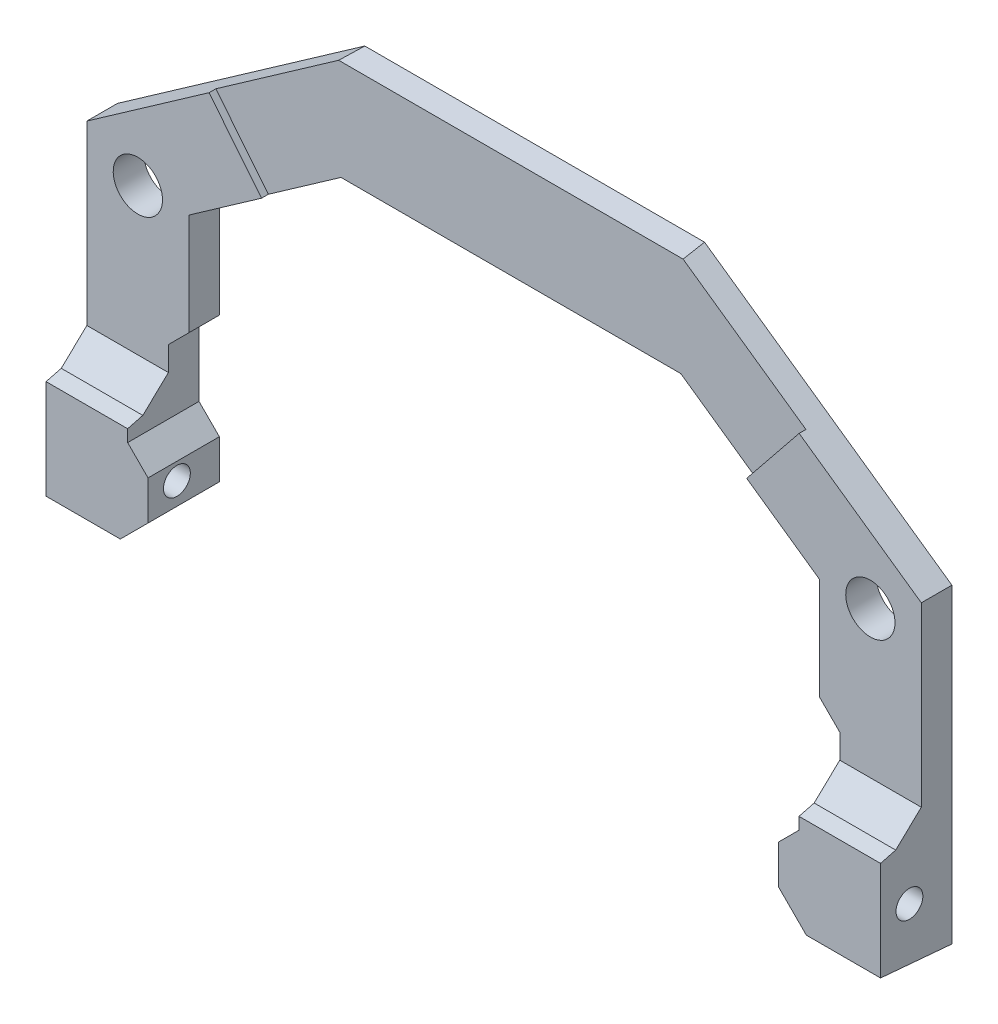
SolidWorks part; units mm, degrees
ref_plane "Front Plane" through (0, 0, 0) normal (0, 0, 1) x (1, 0, 0)
ref_plane "Top Plane" through (0, 0, 0) normal (0, 1, 0) x (1, 0, 0)
ref_plane "Right Plane" through (0, 0, 0) normal (1, 0, 0) x (0, 0, -1)
sketch "Sketch1" plane through (0, 0, 0) normal (0, 0, 1) x (1, 0, 0)
  line L0 (0, 0) -> (-31.1912, 0)
  line L1 (-31.1912, 0) -> (-31.1912, -36.195)
  line L2 (-31.1912, -36.195) -> (-23.5712, -36.195)
  line L3 (-23.5712, -36.195) -> (-23.5712, -7.62)
  line L4 (-23.5712, -7.62) -> (0, -7.62)
  line L5 (0, -7.62) -> (0, 0)
  dimension "D1" = 7.62
  dimension "D2" = 7.62
  dimension "D3" = 23.5712
  dimension "D4" = 28.575
extrude "Boss-Extrude1" add sketch "Sketch1" along normal blind 6.35
sketch "Sketch2" plane through (-23.5712, 0, 0) normal (1, 0, 0) x (0, 0, -1)
  line L0 (-3.175, -36.195) -> (-3.175, -20.616) construction
  line L1 (-6.35, -36.195) -> (0, -36.195) construction
  line L2 (-6.35, -7.62) -> (0, -7.62) construction
  circle A0 centre (-3.175, -32.004) radius 1.0033
  dimension "D1" = 2.0066
  dimension "D2" = 24.384
extrude "cut for lid mount screw" cut sketch "Sketch2" against normal through all and the other way through all
sketch "Sketch3" plane through (0, 0, 6.35) normal (0, 0, 1) x (1, 0, 0)
  line L0 (-27.3812, -36.195) -> (-27.3812, 2.9312) construction
  line L1 (-31.1912, -36.195) -> (-23.5712, -36.195) construction
  line L2 (0, 0) -> (-31.1912, 0) construction
  circle A0 centre (-27.3812, -15.24) radius 1.8415
  dimension "D1" = 3.683
  dimension "D2" = 15.24
extrude "cut for mounting screw" cut sketch "Sketch3" against normal through all
mirror "Mirror1" about plane through (0, 0, 0) normal (1, 0, 0) of "Boss-Extrude1"
mirror "Mirror2" about plane through (0, 0, 0) normal (1, 0, 0) of "cut for lid mount screw"
mirror "Mirror3" about plane through (0, 0, 0) normal (1, 0, 0) of "cut for mounting screw"
sketch "Sketch4" plane through (0, 0, 6.35) normal (0, 0, 1) x (1, 0, 0)
  line L0 (-25.0952, -24.384) -> (-25.0952, -29.2079)
  line L1 (-23.5712, -36.195) -> (-23.5712, -7.62) construction
  line L2 (-25.0952, -29.2079) -> (-23.5712, -30.7319)
  line L3 (-23.5712, -22.86) -> (-23.5712, -30.7319)
  line L4 (-23.5712, -36.195) -> (-23.5712, -33.655)
  line L7 (-25.0952, -24.384) -> (-23.5712, -22.86)
  line L8 (-23.5712, -33.655) -> (-26.1112, -36.195)
  line L10 (-23.5712, -7.62) -> (23.5712, -7.62) construction
  line L11 (-31.1912, -36.195) -> (-23.5712, -36.195) construction
  line L12 (-26.1112, -36.195) -> (-23.5712, -36.195)
  dimension "D1" = 135
  dimension "D2" = 135
  dimension "D3" = 1.524
  dimension "D4" = 15.24
  dimension "D5" = 2.54
  dimension "D6" = 2.54
extrude "cut for control wire clearance" cut sketch "Sketch4" against normal through all
mirror "Mirror4" about plane through (0, 0, 0) normal (1, 0, 0) of "cut for control wire clearance"
sketch "Sketch5" plane through (0, 0, 6.35) normal (0, 0, 1) x (1, 0, 0)
  line L0 (-23.5712, -15.24) -> (-12.7, -7.62)
  line L1 (-23.5712, -22.86) -> (-23.5712, -7.62) construction
  line L2 (-23.5712, -7.62) -> (23.5712, -7.62) construction
  line L3 (-31.1912, -12.5421) -> (-13.2978, 0)
  line L4 (-31.1912, 0) -> (-31.1912, -36.195) construction
  line L5 (31.1912, 0) -> (-31.1912, 0) construction
  line L6 (-12.7, -7.62) -> (-13.2978, 0)
  line L7 (-31.1912, -12.5421) -> (-25.1687, -12.5421)
  line L8 (-25.1687, -12.5421) -> (-23.5712, -15.24)
  point P6 (0, -7.62)
  dimension "D1" = 12.7
extrude "Boss-Extrude2" add sketch "Sketch5" against normal blind 6.35
sketch "Sketch6" plane through (0, 0, 6.35) normal (0, 0, 1) x (1, 0, 0)
  line L0 (-12.7, 0) -> (-31.1912, -12.9611)
  line L1 (31.1912, 0) -> (-31.1912, 0) construction
  line L2 (-31.1912, 0) -> (-31.1912, -36.195) construction
  line L3 (-31.1912, -12.9611) -> (-31.1912, 0)
  line L4 (-31.1912, 0) -> (-12.7, 0)
  line L5 (-23.5712, -15.24) -> (-12.7, -7.62) construction
extrude "Cut-Extrude1" cut sketch "Sketch6" against normal through all
mirror "Mirror5" about plane through (0, 0, 0) normal (1, 0, 0) of "Cut-Extrude1", "Boss-Extrude2"
sketch "Sketch7" plane through (-31.1912, 0, 0) normal (-1, 0, 0) x (0, 0, 1)
  line L0 (6.35, -28.575) -> (4.2015, -28.0124)
  line L1 (6.35, -12.9611) -> (6.35, -36.195) construction
  line L2 (4.2015, -28.0124) -> (2.286, -26.1971)
  line L3 (0, 0) -> (2.286, -0.1562)
  line L4 (0, 0) -> (6.35, 0) construction
  line L5 (2.286, -0.1562) -> (2.286, -26.1971)
  line L6 (6.35, 0) -> (6.35, -28.575)
  line L9 (0, -36.195) -> (6.35, -36.195)
  line L10 (0, -36.195) -> (6.35, -35.6394)
  line L11 (6.35, -35.6394) -> (6.35, -36.195)
  line L12 (0, -12.9611) -> (0, 0) construction
  line L13 (0, 0) -> (6.35, 0)
  dimension "D1" = 2.286
  dimension "D2" = 5
extrude "Cut-Extrude2" cut sketch "Sketch7" against normal through all
sketch "Sketch18" plane through (31.1912, 0, 0) normal (1, 0, 0) x (0, 0, -1)
  line L0 (-6.35, -27.5148) -> (-5.334, -27.5148)
  line L1 (-5.334, -27.5148) -> (-5.334, -36.4592)
  line L2 (-5.334, -36.4592) -> (-6.35, -36.4592)
  line L3 (-6.35, -36.4592) -> (-6.35, -27.5148)
  dimension "D1" = 1.016
extrude "Cut-Extrude11" cut sketch "Sketch18" against normal through all
sketch "Sketch19" plane through (0, 0, 2.286) normal (0, 0, 1) x (1, 0, 0)
  line L0 (-22.057, -6.5587) -> (-18.1356, -11.43)
  line L1 (-31.1912, -12.9611) -> (-12.9229, -0.1562) construction
  line L2 (-23.5712, -15.24) -> (-12.7, -7.62) construction
  line L3 (-18.1356, -11.43) -> (-12.7, -7.62)
  line L4 (-12.7, -7.62) -> (0, -7.62)
  line L5 (12.7, -7.62) -> (-12.7, -7.62) construction
  line L6 (0, -7.62) -> (0, 0)
  line L7 (0, 0) -> (-12.7, 0)
  line L8 (-12.7, 0) -> (-22.057, -6.5587)
extrude "Cut-Extrude12" cut sketch "Sketch19" against normal blind 0.508
mirror "Mirror6" about plane through (0, 0, 0) normal (1, 0, 0) of "Cut-Extrude12"
